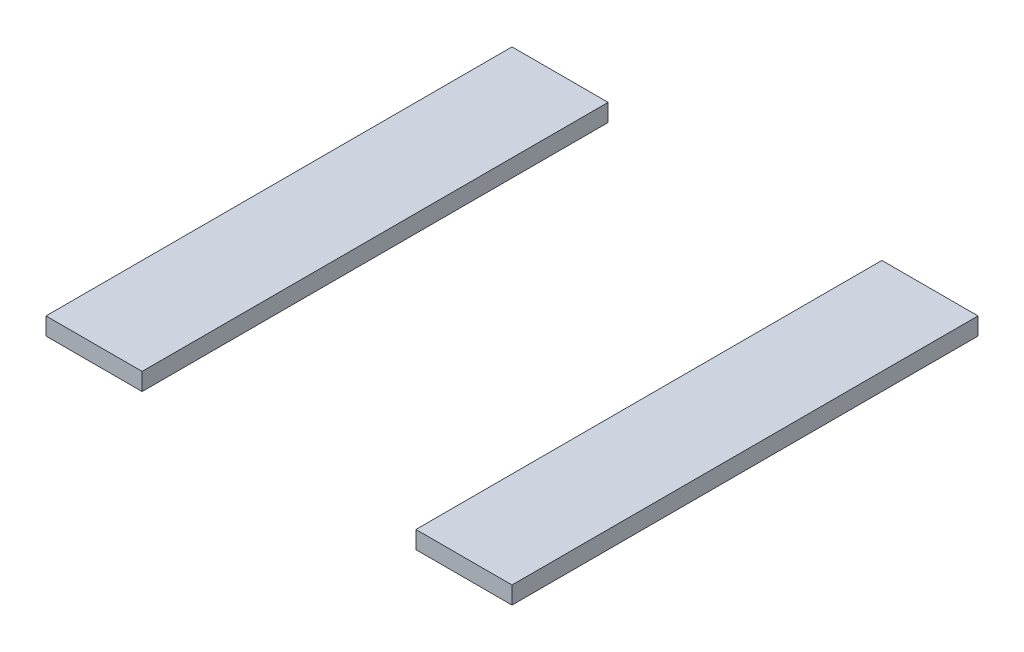
SolidWorks part; units mm, degrees
ref_plane "Front Plane" through (0, 0, 0) normal (0, 0, 1) x (1, 0, 0)
ref_plane "Top Plane" through (0, 0, 0) normal (0, 1, 0) x (1, 0, 0)
ref_plane "Right Plane" through (0, 0, 0) normal (1, 0, 0) x (0, 0, -1)
sketch "Sketch1" plane through (0, 0, 0) normal (0, 1, 0) x (1, 0, 0)
  line L0 (-63.5, 0) -> (-63.5, 80)
  line L1 (0, 0) -> (-80, 0) construction
  line L2 (0, 0) -> (0, 80)
  line L3 (0, 80) -> (-80, 80) construction
  line L4 (-80, 0) -> (-80, 80)
  line L5 (-16.5, 0) -> (-16.5, 80)
  line L7 (-40, 0) -> (-40, 80) construction
  line L8 (-16.5, 0) -> (-16.5, 80) construction
  line L9 (-63.5, 0) -> (-63.5, 80) construction
  line L10 (0, 80) -> (-16.5, 80)
  line L11 (-63.5, 80) -> (-80, 80)
  line L12 (-80, 0) -> (-63.5, 0)
  line L13 (-16.5, 0) -> (0, 0)
sketch "Sketch2" plane through (0, 0, 0) normal (1, 0, 0) x (0, 0, -1)
  line L1 (80, -3) -> (0, -3)
  line L2 (80, -3) -> (80, 0)
  line L3 (80, 0) -> (0, 0)
  line L4 (0, -3) -> (0, 0)
extrude "Boss-Extrude1" add sketch "Sketch1" against normal up to vertex (3 mm away) up to point (0, -3, 0)
